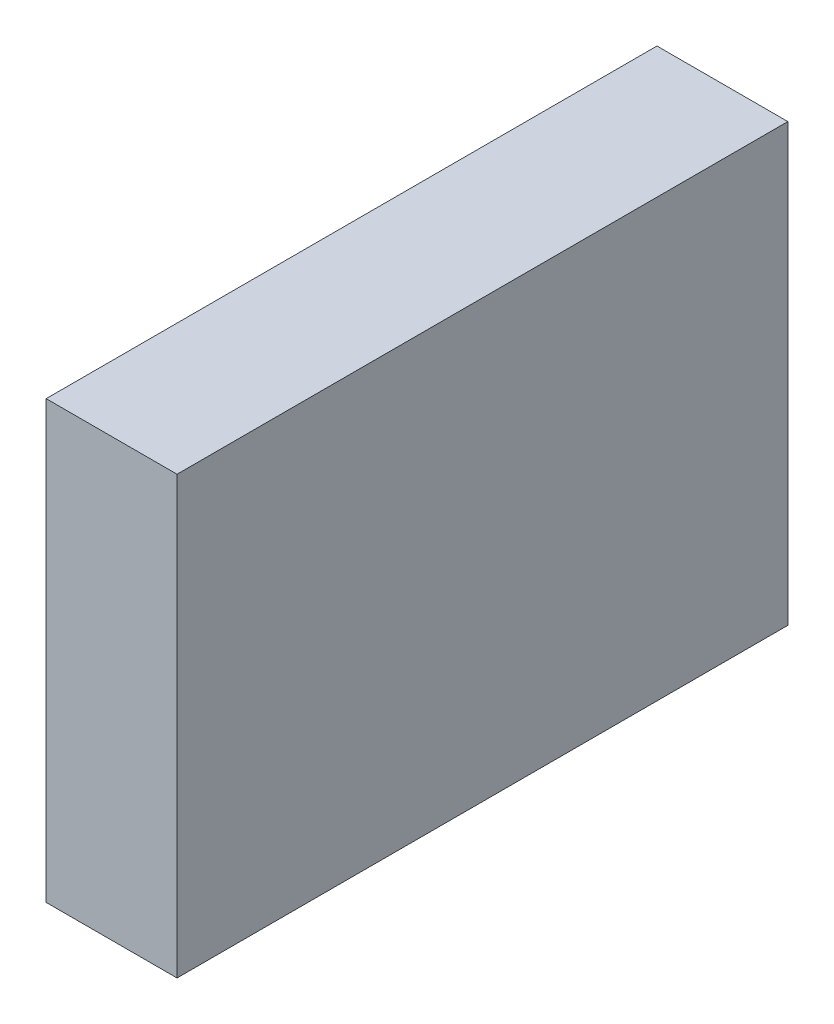
SolidWorks part; units mm, degrees
ref_plane "Front Plane" through (0, 0, 0) normal (0, 0, 1) x (1, 0, 0)
ref_plane "Top Plane" through (0, 0, 0) normal (0, 1, 0) x (1, 0, 0)
ref_plane "Right Plane" through (0, 0, 0) normal (1, 0, 0) x (0, 0, -1)
sketch "Sketch1" plane through (0, 0, 0) normal (0, 1, 0) x (1, 0, 0)
  line L1 (-9.525, -44.45) -> (9.525, -44.45)
  line L2 (-9.525, -44.45) -> (-9.525, 44.45)
  line L3 (-9.525, 44.45) -> (9.525, 44.45)
  line L4 (9.525, -44.45) -> (9.525, 44.45)
  line L5 (-9.525, -44.45) -> (9.525, 44.45) construction
  line L6 (-9.525, 44.45) -> (9.525, -44.45) construction
  point P0 (0, 0)
  dimension "D1" = 19.05
  dimension "D2" = 88.9
extrude "Boss-Extrude1" add sketch "Sketch1" along normal blind 63.5
